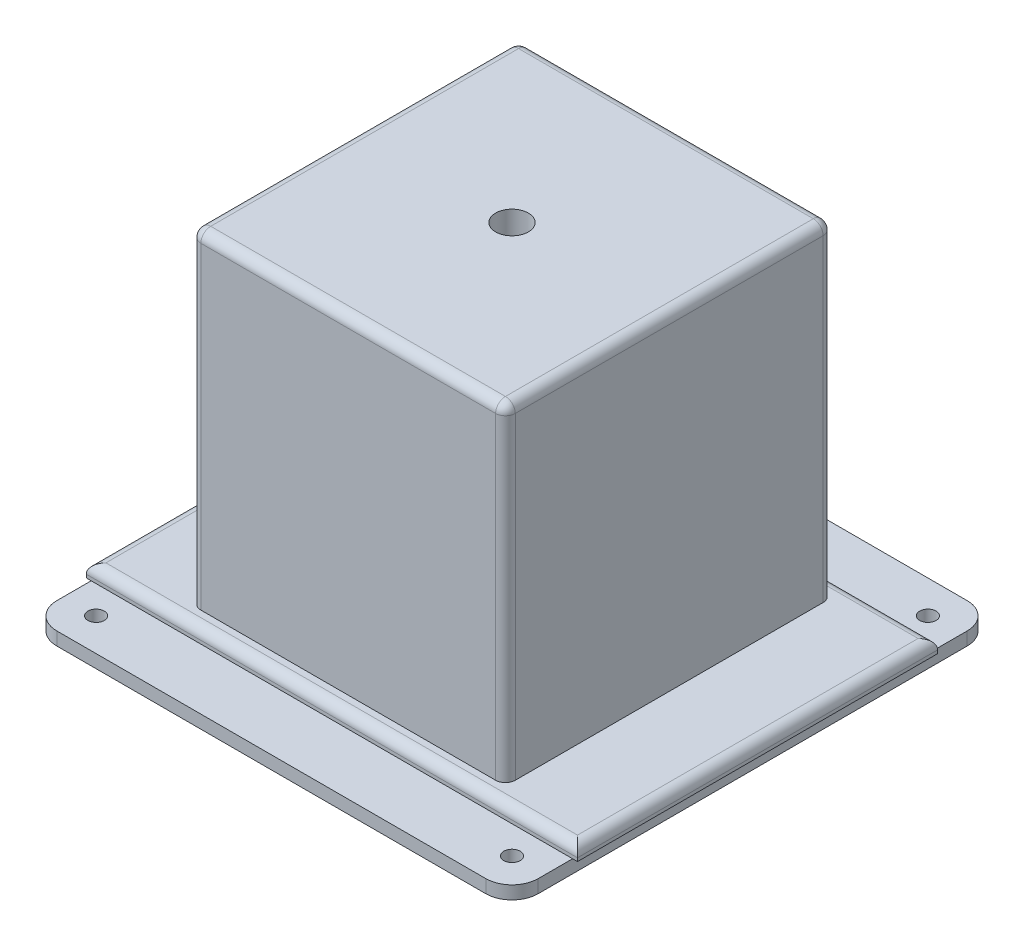
SolidWorks part; units mm, degrees
ref_plane "Front Plane" through (0, 0, 0) normal (0, 0, 1) x (1, 0, 0)
ref_plane "Top Plane" through (0, 0, 0) normal (0, 1, 0) x (1, 0, 0)
ref_plane "Right Plane" through (0, 0, 0) normal (1, 0, 0) x (0, 0, -1)
sketch "Sketch1" plane through (0, 0, 0) normal (0, 1, 0) x (1, 0, 0)
  line L1 (0, 0) -> (150, 0)
  line L2 (0, 0) -> (0, 110)
  line L3 (0, 110) -> (150, 110)
  line L4 (150, 0) -> (150, 110)
  dimension "D1" = 110
  dimension "D2" = 150
extrude "Boss-Extrude1" add sketch "Sketch1" along normal blind 4
sketch "Sketch2" plane through (0, 4, 0) normal (0, 1, 0) x (1, 0, 0)
  line L0 (0, 0) -> (150, 0) construction
  line L1 (27, 105) -> (123, 105)
  line L2 (27, 105) -> (27, 5)
  line L3 (27, 5) -> (123, 5)
  line L4 (123, 105) -> (123, 5)
  line L5 (150, 110) -> (0, 110) construction
  line L6 (150, 0) -> (150, 110) construction
  line L7 (0, 110) -> (0, 0) construction
  dimension "D1" = 5
  dimension "D2" = 5
  dimension "D3" = 27
  dimension "D4" = 27
extrude "Boss-Extrude2" add sketch "Sketch2" along normal blind 100
fillet "Fillet1" radius 3 12 edges at (150, 4, -55) (75, 4, 0) (0, 4, -55) (75, 4, -110) (75, 104, -5) (123, 104, -55) (75, 104, -105) (27, 104, -55) (27, 54, -105) (27, 54, -5) (123, 54, -5) (123, 54, -105)
sketch "Sketch4" plane through (0, 104, 0) normal (0, 1, 0) x (1, 0, 0)
  circle A0 centre (75, 55) radius 5
  dimension "D1" = 10
extrude "Cut-Extrude1" cut sketch "Sketch4" against normal blind 15
sketch "Sketch5" plane through (0, 0, 0) normal (0, -1, 0) x (1, 0, 0)
  line L0 (0, 0) -> (150, 0) construction
  line L1 (1.5, 18.5) -> (148.5, 18.5)
  line L2 (1.5, 18.5) -> (1.5, -128.5)
  line L3 (1.5, -128.5) -> (148.5, -128.5)
  line L4 (148.5, 18.5) -> (148.5, -128.5)
  line L5 (150, 0) -> (150, -110) construction
  point P6 (75, 0)
  point P7 (75, 18.5)
  point P10 (150, -55)
  point P11 (148.5, -55)
  dimension "D1" = 147
  dimension "D2" = 147
extrude "Boss-Extrude3" add sketch "Sketch5" along normal blind 4
sketch "Sketch6" plane through (0, 0, 0) normal (0, 1, 0) x (1, 0, 0)
  line L0 (1.5, 128.5) -> (148.5, 128.5) construction
  line L2 (1.5, 110) -> (1.5, 128.5) construction
  line L3 (148.5, -18.5) -> (1.5, -18.5) construction
  line L4 (148.5, 128.5) -> (148.5, 110) construction
  circle A0 centre (11.5, 118.5) radius 2.5
  circle A1 centre (138.5, 118.5) radius 2.5
  circle A2 centre (11.5, -8.5) radius 2.5
  circle A3 centre (138.5, -8.5) radius 2.5
  point P12 (1.5, 116.3688)
  point P13 (0, 0)
  point P14 (0, 0)
  point P15 (0, 0)
  point P20 (0, 0)
  dimension "D1" = 5
  dimension "D2" = 10
  dimension "D3" = 10
  dimension "D4" = 10
  dimension "D5" = 10
extrude "Cut-Extrude2" cut sketch "Sketch6" against normal through all
fillet "Fillet2" radius 8 4 edges at (1.5, -2, 18.5) (148.5, -2, 18.5) (148.5, -2, -128.5) (1.5, -2, -128.5)
